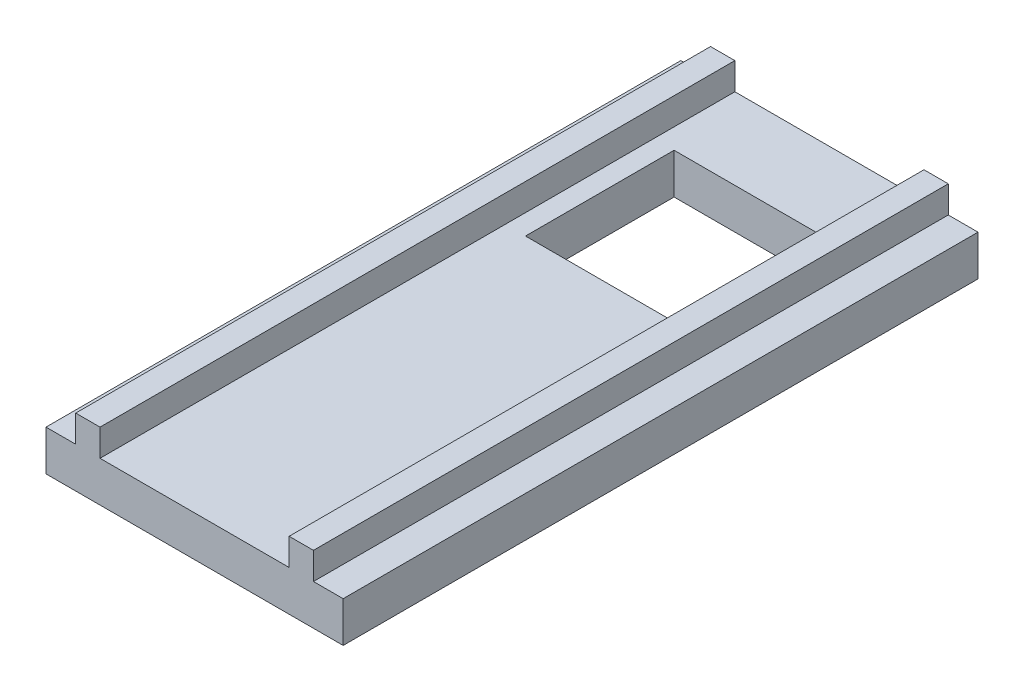
SolidWorks part; units mm, degrees
ref_plane "Front Plane" through (0, 0, 0) normal (0, 0, 1) x (1, 0, 0)
ref_plane "Top Plane" through (0, 0, 0) normal (0, 1, 0) x (1, 0, 0)
ref_plane "Right Plane" through (0, 0, 0) normal (1, 0, 0) x (0, 0, -1)
sketch "Sketch1" plane through (0, 0, 0) normal (0, 1, 0) x (1, 0, 0)
  line L0 (-8, 19.5) -> (-7, 20.5) construction
  line L5 (-11, -23.5) -> (11, -23.5)
  line L6 (-11, -23.5) -> (-11, 23.5)
  line L7 (-11, 23.5) -> (11, 23.5)
  line L8 (11, -23.5) -> (11, 23.5)
  line L9 (0, 23.5) -> (0, -23.5) construction
  line L10 (-11, 0) -> (11, 0) construction
  line L11 (-11, 23.5) -> (-8, 23.5) construction
  line L12 (-11, 23.5) -> (-11, 20.5) construction
  line L13 (-11, 20.5) -> (-8, 20.5) construction
  line L14 (-8, 23.5) -> (-8, 20.5) construction
  line L19 (-8, 20.5) -> (-7, 20.5) construction
  line L20 (-8, 20.5) -> (-8, 19.5) construction
  line L21 (-8, 19.5) -> (-7, 19.5) construction
  line L22 (-7, 20.5) -> (-7, 19.5) construction
  line L23 (-8, 20.5) -> (-7, 19.5) construction
  line L24 (7.5, 20) -> (11, 20) construction
  line L25 (-7, 19.5) -> (-7, 23.5) construction
  line L27 (-5.5, 6.5) -> (5.5, 6.5)
  line L28 (-5.5, 6.5) -> (-5.5, 17.5)
  line L29 (-5.5, 17.5) -> (5.5, 17.5)
  line L30 (5.5, 6.5) -> (5.5, 17.5)
  line L31 (0, 17.5) -> (0, 6.5) construction
  line L32 (-5.5, 12) -> (5.5, 12) construction
  line L57 (-6.8, -23.5) -> (5.2, -23.5) construction
  circle A0 centre (-7.5, 20) radius 0.5 construction
  circle A1 centre (7.5, 20) radius 0.5 construction
  circle A2 centre (7.5, -20) radius 0.5 construction
  circle A3 centre (-7.5, -20) radius 0.5 construction
  point P0 (0, 0)
  point P18 (0, 12)
  dimension "D1" = 1
  dimension "D6" = 4
  dimension "D2" = 3
  dimension "D3" = 47
  dimension "D4" = 22
  dimension "D5" = 3
  dimension "D7" = 11
  dimension "D8" = 6.5
extrude "Boss-Extrude" add sketch "Sketch1" along normal blind 3
sketch "Sketch4" plane through (0, 3, 0) normal (0, 1, 0) x (1, 0, 0)
  line L1 (-6, -16.5) -> (6, -16.5)
  line L2 (-6, -16.5) -> (-6, -23.5)
  line L3 (-6, -23.5) -> (6, -23.5)
  line L4 (6, -16.5) -> (6, -23.5)
  line L5 (-11, -23.5) -> (11, -23.5) construction
  line L6 (0, 23.5) -> (0, -23.5) construction
  point P4 (6.0653, -23.5)
  point P5 (6.0653, -23.5)
  point P8 (0, -16.5)
  point P11 (5.0025, -23.5)
  point P12 (0, -23.5)
  dimension "D1" = 12
  dimension "D2" = 7
sketch "Sketch5" plane through (0, 3, 0) normal (0, 1, 0) x (1, 0, 0)
  line L0 (-11, 23.5) -> (11, 23.5) construction
  line L1 (-7, -23.5) -> (-8.8, -23.5)
  line L2 (-7, -23.5) -> (-7, 23.5)
  line L3 (-7, 23.5) -> (-8.8, 23.5)
  line L4 (-8.8, -23.5) -> (-8.8, 23.5)
  line L5 (-11, -23.5) -> (-11, 23.5) construction
  line L6 (7, -23.5) -> (8.8, -23.5)
  line L7 (7, -23.5) -> (7, 23.5)
  line L8 (7, 23.5) -> (8.8, 23.5)
  line L9 (8.8, -23.5) -> (8.8, 23.5)
  line L10 (-8.8, -23.5) -> (-11, -23.5) construction
  line L11 (8.8, -23.5) -> (11, -23.5) construction
  point P4 (0, 0)
  dimension "D1" = 2.2
  dimension "D2" = 1.8
extrude "Boss-Extrude1" add sketch "Sketch5" along normal blind 2
sketch "Sketch6" plane through (0, 0, 0) normal (0, 1, 0) x (1, 0, 0)
  line L1 (-7, -23.5) -> (-7, 23.5) construction
  line L2 (-8.8, -23.5) -> (-7, -23.5)
  line L3 (-8.8, -23.5) -> (-8.8, -21.4654)
  line L4 (-8.8, -21.4654) -> (-7, -21.4654)
  line L5 (-7, -23.5) -> (-7, -21.4654)
